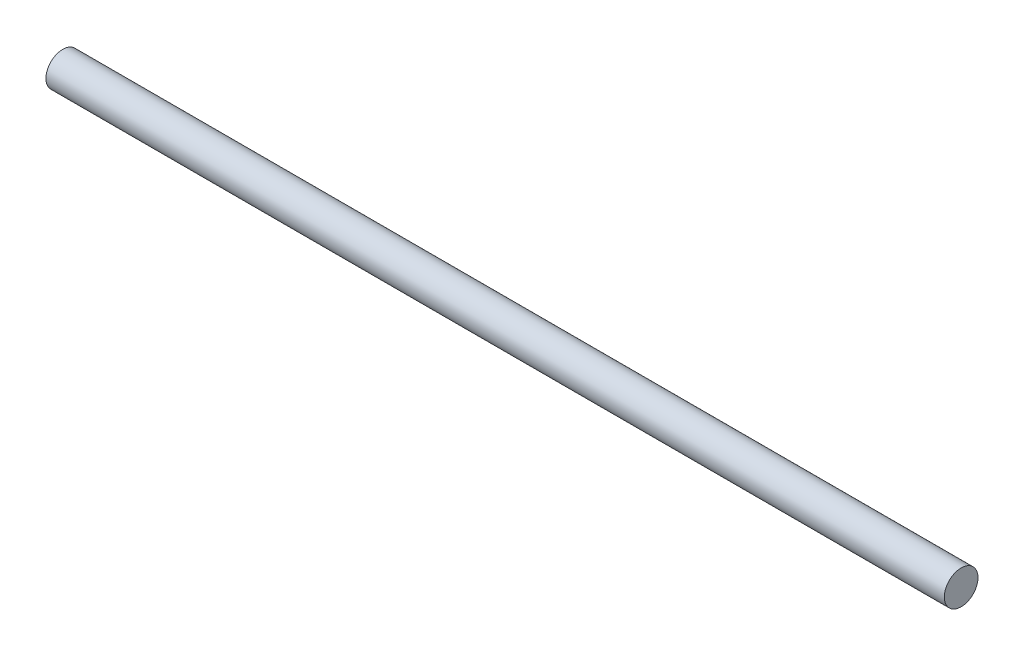
SolidWorks part; units mm, degrees
ref_plane "Plan de face" through (0, 0, 0) normal (0, 0, 1) x (1, 0, 0)
ref_plane "Plan de dessus" through (0, 0, 0) normal (0, 1, 0) x (1, 0, 0)
ref_plane "Plan de droite" through (0, 0, 0) normal (1, 0, 0) x (0, 0, -1)
sketch "Esquisse1" plane through (0, 0, 0) normal (0, 0, 1) x (1, 0, 0)
  line L0 (82.6633, 0) -> (-4.16, 0) construction
  line L1 (0, 0) -> (80, 0)
  line L2 (0, 0) -> (0, 1.5)
  line L3 (0, 1.5) -> (80, 1.5)
  line L4 (80, 0) -> (80, 1.5)
  dimension "D1" = 1.5
  dimension "D2" = 80
revolve "Révolution1" add sketch "Esquisse1" angle 360 about L0
